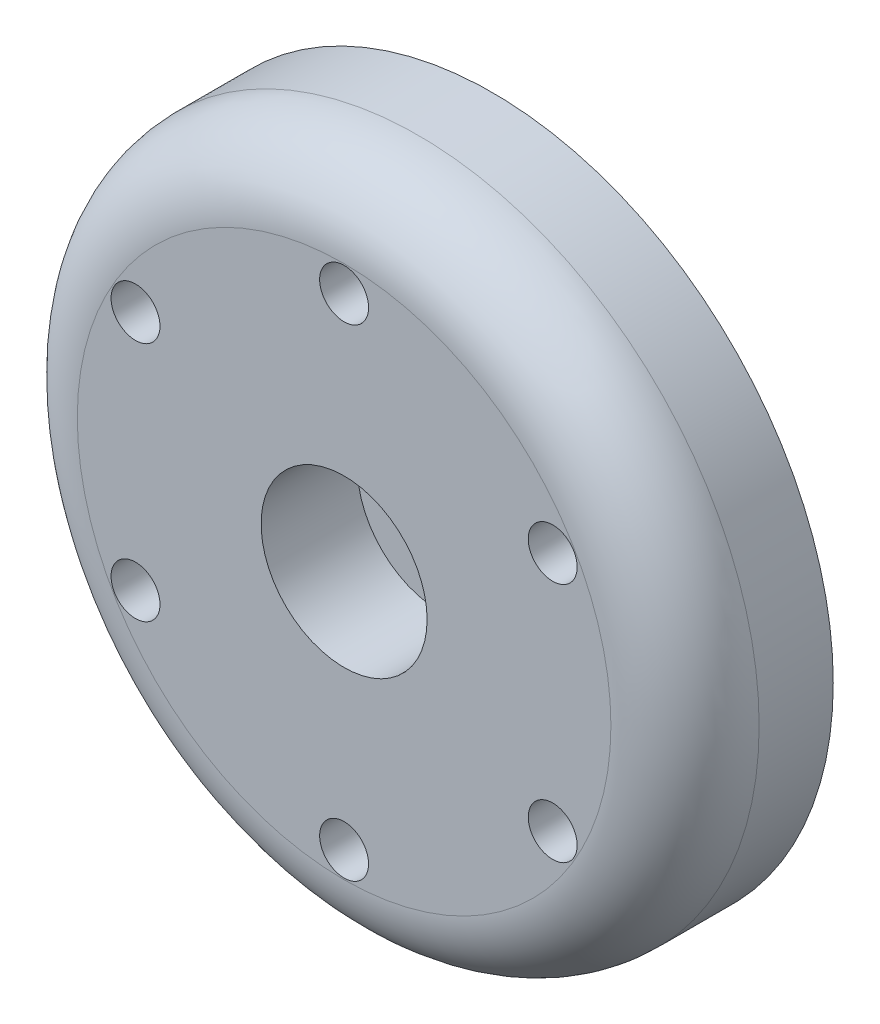
SolidWorks part; units mm, degrees
ref_plane "Front Plane" through (0, 0, 0) normal (0, 0, 1) x (1, 0, 0)
ref_plane "Top Plane" through (0, 0, 0) normal (0, 1, 0) x (1, 0, 0)
ref_plane "Right Plane" through (0, 0, 0) normal (1, 0, 0) x (0, 0, -1)
ref_plane "Plane1" through (0, 0, 0) normal (0, -1, 0) x (1, 0, 0)
sketch "Sketch1" plane through (0, 0, 0) normal (0, -1, 0) x (1, 0, 0)
  line L0 (23, 10) -> (0, 10)
  line L1 (0, 10) -> (0, 0)
  line L2 (0, 0) -> (23, 0)
  line L3 (23, 0) -> (23, 10)
  line L4 (0, 10) -> (0, 0) construction
revolve "Revolve1" add sketch "Sketch1" angle 360 about L4
hole_wizard "Hole1" positions "Sketch3" profile "Sketch2" legacy
sketch "Sketch3" plane through (0, 0, 0) normal (0, 0, -1) x (-1, 0, 0)
  point P0 (0, 0)
sketch "Sketch2" plane through (0, 0, 0) normal (1, 0, 0) x (0, 1, 0)
  line L0 (0, 0) -> (0, 5.8)
  line L1 (0, 5.8) -> (20, 5.8)
  line L2 (20, 5.8) -> (20, 0)
  line L3 (20, 0) -> (0, 0)
  line L4 (0, 110) -> (0, -10) construction
  dimension "Diameter" = 40
  dimension "Depth" = 5.8
sketch "Sketch4" plane through (0, 0, 0) normal (0, -1, 0) x (1, 0, 0)
  line L0 (12.5, 5.8) -> (0, 5.8)
  line L1 (0, 5.8) -> (0, 0)
  line L2 (0, 0) -> (12.5, 0)
  line L3 (12.5, 0) -> (12.5, 5.8)
  line L4 (0, 5.8) -> (0, 0) construction
revolve "Revolve2" add sketch "Sketch4" angle 360 about L4
hole_wizard "#4 Clearance Hole1" positions "Sketch6" profile "Sketch5" hole size "#4" standard "ANSI Inch"
sketch "Sketch6" plane through (0, 0, 10) normal (0, 0, 1) x (1, 0, 0)
  point P0 (14.0729, 8.125)
  point P1 (14.0729, -8.125)
  point P2 (0, -16.25)
  point P3 (-14.0729, -8.125)
  point P4 (-14.0729, 8.125)
  point P5 (0, 16.25)
sketch "Sketch5" plane through (14.0729, 8.125, 10) normal (1, 0, 0) x (0, -1, 0)
  line L0 (0, 0) -> (0, 10)
  line L1 (0, 10) -> (1.65, 10)
  line L2 (1.65, 10) -> (1.65, 0)
  line L5 (1.65, 0) -> (0, 0)
  line L11 (0, -6.35) -> (0, 107.95) construction
  dimension "Thru Hole Dia." = 3.3
  dimension "Thru Hole Depth" = 10
hole_wizard "CBORE for #12 Binding Head Machine Screw1" positions "Sketch8" profile "Sketch7" counterbore size "#12" standard "ANSI Inch"
sketch "Sketch8" plane through (0, 0, 10) normal (0, 0, 1) x (1, 0, 0)
  point P0 (0, 0)
sketch "Sketch7" plane through (0, 0, 10) normal (1, 0, 0) x (0, -1, 0)
  line L0 (0, 0) -> (0, 10)
  line L1 (0, 10) -> (3.0225, 10)
  line L3 (3.0225, 10) -> (3.0225, 6.5)
  line L4 (3.0225, 6.5) -> (5.6, 6.5)
  line L5 (5.6, 6.5) -> (5.6, 0)
  line L7 (5.6, 0) -> (0, 0)
  line L11 (0, -6.35) -> (0, 107.95) construction
  dimension "Thru Hole Dia." = 6.045
  dimension "Thru Hole Depth" = 10
  dimension "C'Bore Dia." = 11.2
  dimension "C'Bore Depth" = 6.5
fillet "Fillet1" radius 5 1 edges at (-23, 0, 10)
